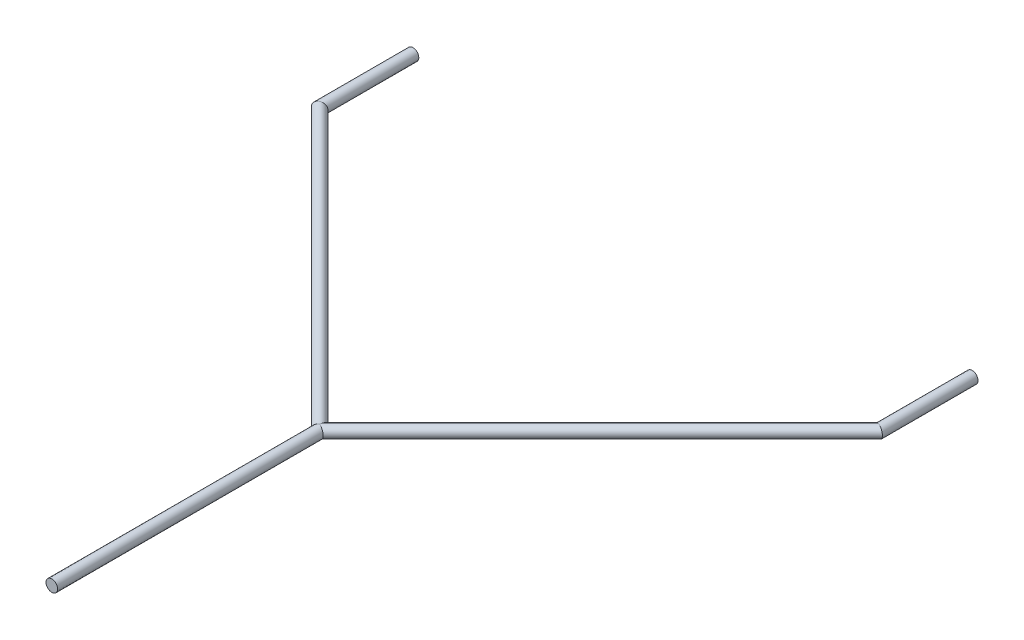
SolidWorks part; units mm, degrees
ref_plane "Front Plane" through (0, 0, 0) normal (0, 0, 1) x (1, 0, 0)
ref_plane "Top Plane" through (0, 0, 0) normal (0, 1, 0) x (1, 0, 0)
ref_plane "Right Plane" through (0, 0, 0) normal (1, 0, 0) x (0, 0, -1)
sketch "Sketch1" plane through (0, 0, 0) normal (0, 1, 0) x (1, 0, 0)
  line L0 (0, 0) -> (0, 73.025)
  line L1 (0, 73.025) -> (76.2, 149.225)
  line L2 (76.2, 149.225) -> (-76.2, 149.225) construction
  line L3 (-76.2, 149.225) -> (0, 73.025)
  line L4 (-76.2, 149.225) -> (-76.2, 174.625)
  line L5 (76.2, 149.225) -> (76.2, 174.625)
  dimension "D1" = 76.2
  dimension "D2" = 76.2
  dimension "D3" = 73.025
  dimension "D4" = 25.4
  dimension "D5" = 25.4
sketch "Sketch2" plane through (0, 0, 0) normal (0, 0, 1) x (1, 0, 0)
  circle A0 centre (0, 0) radius 1.5875
  dimension "D1" = 3.175
sweep "Sweep1" add profiles "Sketch2" path "Sketch1"
ref_plane "Plane1" through (-76.2, 0, -174.625) normal (0, 0, 1) x (1, 0, 0)
sketch "Sketch3" plane through (-76.2, 0, -174.625) normal (0, 0, 1) x (1, 0, 0)
  circle A0 centre (0, 0) radius 1.5875
  dimension "D1" = 3.175
sketch "Sketch4" plane through (0, 0, 0) normal (0, 1, 0) x (1, 0, 0)
  line L0 (-76.2, 174.625) -> (-76.2, 149.225)
  line L1 (-76.2, 149.225) -> (0, 73.025)
sweep "Sweep4" add profiles "Sketch3" path "Sketch4"
